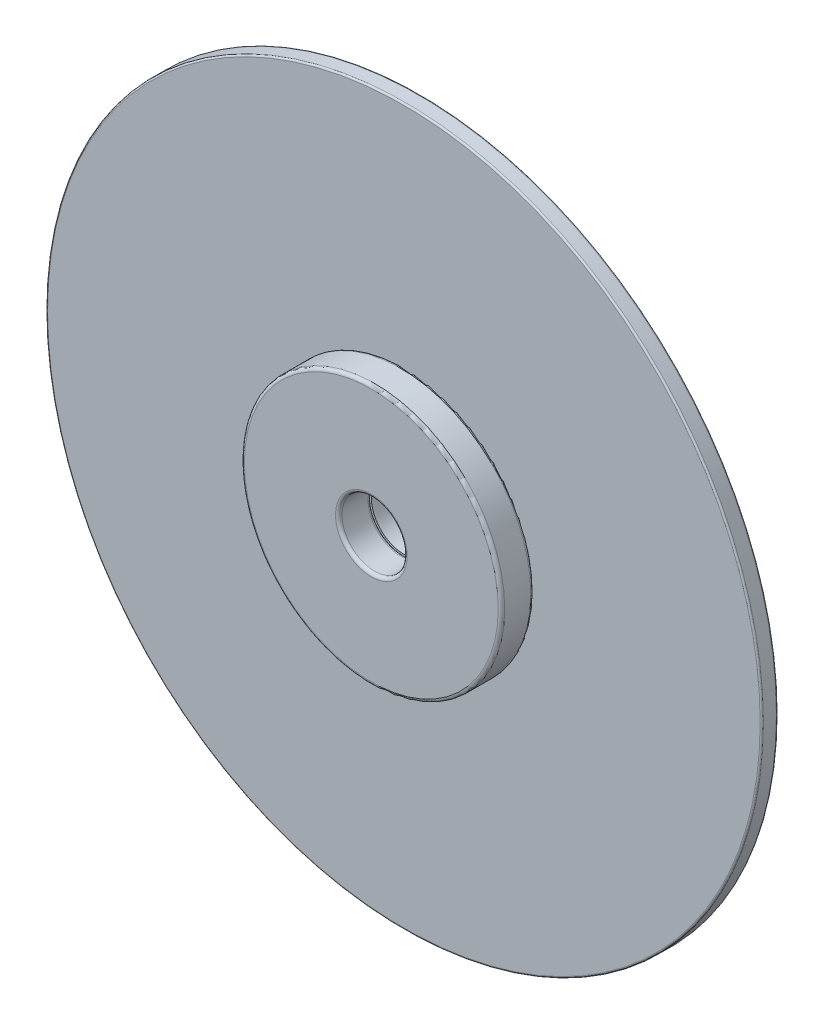
SolidWorks part; units mm, degrees
ref_plane "Ön Düzlem" through (0, 0, 0) normal (0, 0, 1) x (1, 0, 0)
ref_plane "Üst Düzlem" through (0, 0, 0) normal (0, 1, 0) x (1, 0, 0)
ref_plane "Sağ Düzlem" through (0, 0, 0) normal (1, 0, 0) x (0, 0, -1)
sketch "Sketch2" plane through (0, 0, 0) normal (0, 0, 1) x (1, 0, 0)
  circle A0 centre (0, 0) radius 11
  circle A1 centre (0, 0) radius 1
  dimension "D1" = 22
  dimension "D2" = 2
extrude "Boss-Extrude1" add sketch "Sketch2" along normal blind 0.5
sketch "Sketch3" plane through (0, 0, 0.5) normal (0, 0, 1) x (1, 0, 0)
  circle A0 centre (0, 0) radius 4
  circle A1 centre (0, 0) radius 1
  dimension "D1" = 8
  dimension "D2" = 2
extrude "Boss-Extrude2" add sketch "Sketch3" along normal blind 1 separate body
sketch "Sketch4" plane through (0, 0, 0) normal (0, 0, -1) x (-1, 0, 0)
  circle A0 centre (0, 0) radius 4
  circle A1 centre (0, 0) radius 1
  dimension "D1" = 8
extrude "Boss-Extrude3" add sketch "Sketch4" along normal blind 1 separate body
fillet "Fillet1" radius 0.1 3 edges at (-1, 0, -1) (-4, 0, 0) (-4, 0, -1)
fillet "Fillet2" radius 0.1 4 edges at (1, 0, 0.5) (4, 0, 0.5) (1, 0, 1.5) (4, 0, 1.5)
fillet "Fillet3" radius 0.05 2 edges at (11, 0, 0) (11, 0, 0.5)
